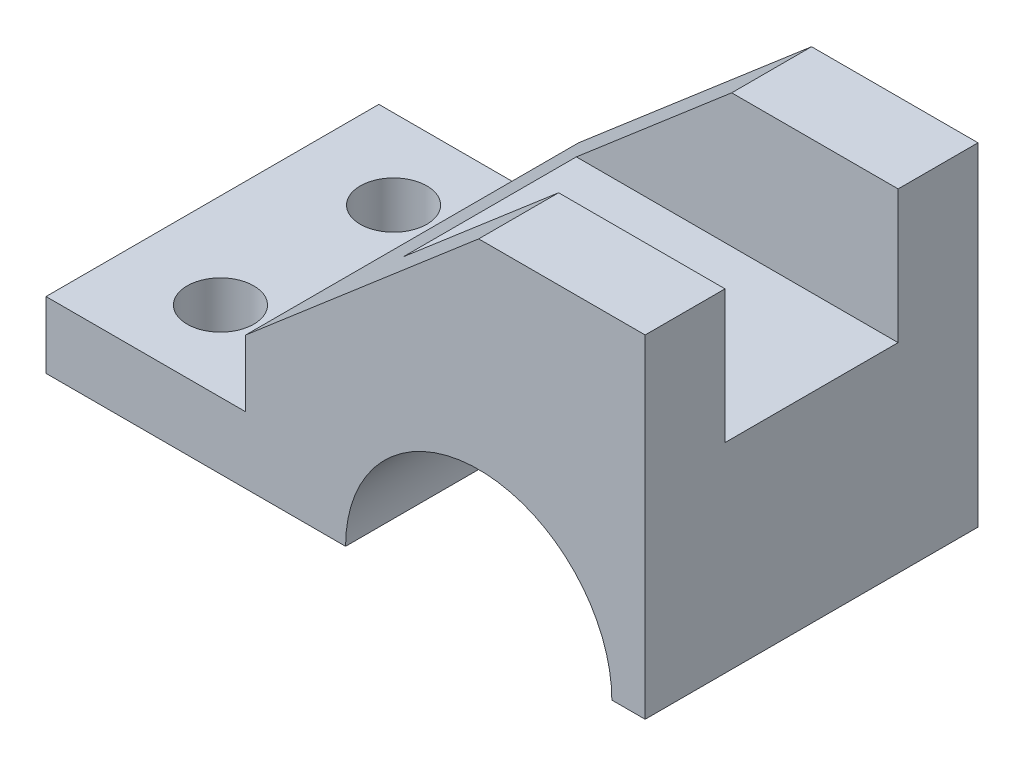
SolidWorks part; units mm, degrees
ref_plane "Alzado" through (0, 0, 0) normal (0, 0, 1) x (1, 0, 0)
ref_plane "Planta" through (0, 0, 0) normal (0, 1, 0) x (1, 0, 0)
ref_plane "Vista lateral" through (0, 0, 0) normal (1, 0, 0) x (0, 0, -1)
sketch "Croquis1" plane through (0, 0, 0) normal (0, 0, 1) x (1, 0, 0)
  line L0 (-68.9206, -21.5896) -> (-23.9206, -21.5896)
  line L1 (16.0794, -21.5896) -> (21.0794, -21.5896)
  line L2 (21.0794, -21.5896) -> (21.0794, 28.4104)
  line L3 (21.0794, 28.4104) -> (-3.9206, 28.4104)
  line L4 (-68.9206, -21.5896) -> (-68.9206, -11.5896)
  line L5 (-68.9206, -11.5896) -> (-38.9206, -11.5896)
  line L6 (-38.9206, -11.5896) -> (-38.9206, -1.5896)
  line L7 (-38.9206, -1.5896) -> (-3.9206, 28.4104)
  arc A0 (-23.9206, -21.5896) -> (16.0794, -21.5896) centre (-3.9206, -21.5896) cw
extrude "Saliente-Extruir2" add sketch "Croquis1" against normal blind 50
sketch "Croquis3" plane through (0, -11.5896, 0) normal (0, 1, 0) x (1, 0, 0)
  line L0 (-68.9206, 25) -> (-38.9206, 25) construction
  line L1 (-68.9206, 50) -> (-68.9206, 0) construction
  line L2 (-38.9206, 50) -> (-38.9206, 0) construction
  line L3 (-38.9206, 50) -> (-68.9206, 50) construction
  circle A0 centre (-54.7121, 38) radius 5
  circle A1 centre (-54.7121, 12) radius 5
  dimension "D1" = 10
  dimension "D2" = 12
extrude "Cortar-Extruir3" cut sketch "Croquis3" against normal blind 10
sketch "Croquis5" plane through (21.0794, 0, 0) normal (1, 0, 0) x (0, 0, -1)
  line L0 (12, 28.4104) -> (12, 8.4104)
  line L1 (12, 8.4104) -> (38, 8.4104)
  line L2 (38, 8.4104) -> (38, 28.4104)
  line L3 (38, 28.4104) -> (12, 28.4104)
extrude "Cortar-Extruir4" cut sketch "Croquis5" against normal blind 100
